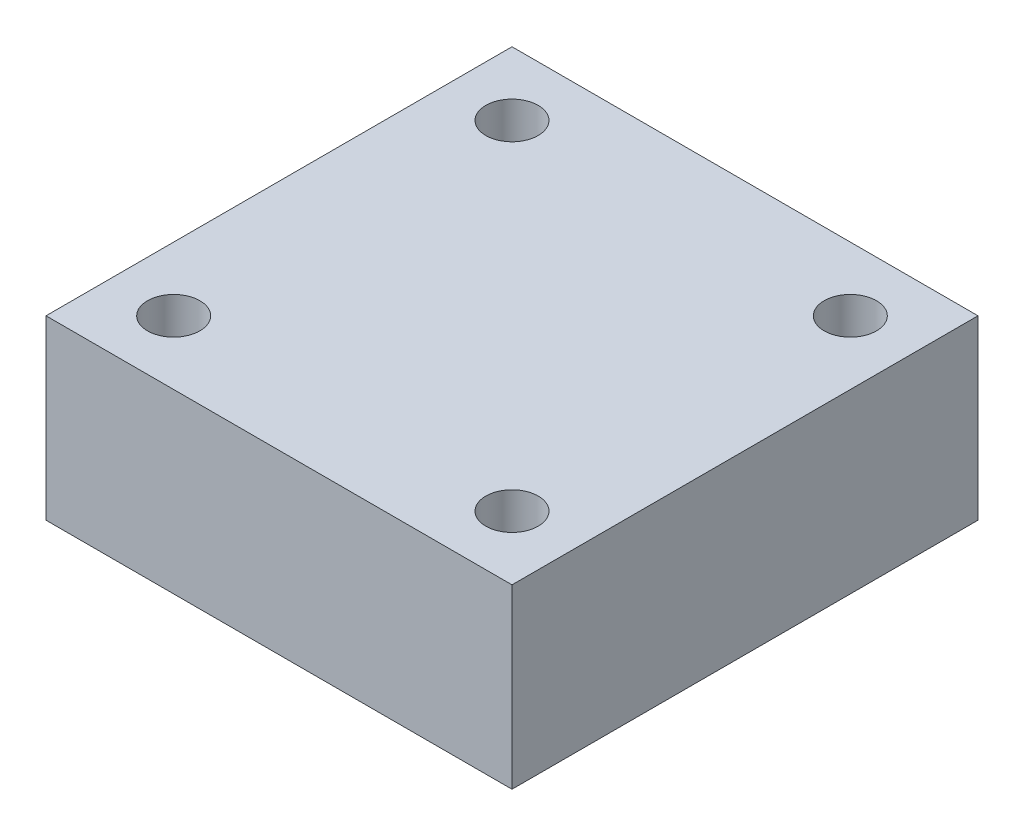
SolidWorks part; units mm, degrees
ref_plane "Front" through (0, 0, 0) normal (0, 0, 1) x (1, 0, 0)
ref_plane "Top" through (0, 0, 0) normal (0, 1, 0) x (1, 0, 0)
ref_plane "Right" through (0, 0, 0) normal (1, 0, 0) x (0, 0, -1)
sketch "Sketch1" plane through (0, 0, 0) normal (0, 1, 0) x (1, 0, 0)
  line L1 (-26.5, -26.5) -> (26.5, -26.5) construction
  line L2 (-26.5, -26.5) -> (-26.5, 26.5) construction
  line L3 (-26.5, 26.5) -> (26.5, 26.5) construction
  line L4 (26.5, -26.5) -> (26.5, 26.5) construction
  line L5 (-26.5, -26.5) -> (26.5, 26.5) construction
  line L6 (-26.5, 26.5) -> (26.5, -26.5) construction
  line L7 (-36.5, -36.5) -> (36.5, -36.5)
  line L8 (-36.5, -36.5) -> (-36.5, 36.5)
  line L9 (-36.5, 36.5) -> (36.5, 36.5)
  line L10 (36.5, -36.5) -> (36.5, 36.5)
  line L11 (-36.5, -36.5) -> (36.5, 36.5) construction
  line L12 (-36.5, 36.5) -> (36.5, -36.5) construction
  circle A0 centre (-26.5, 26.5) radius 4.1
  circle A1 centre (26.5, 26.5) radius 4.1
  circle A2 centre (26.5, -26.5) radius 4.1
  circle A3 centre (-26.5, -26.5) radius 4.1
  point P0 (0, 0)
  point P6 (0, 0)
  dimension "D3" = 8.2
  dimension "D1" = 53
  dimension "D2" = 73
extrude "Boss-Extrude1" add sketch "Sketch1" along normal blind 27.734
